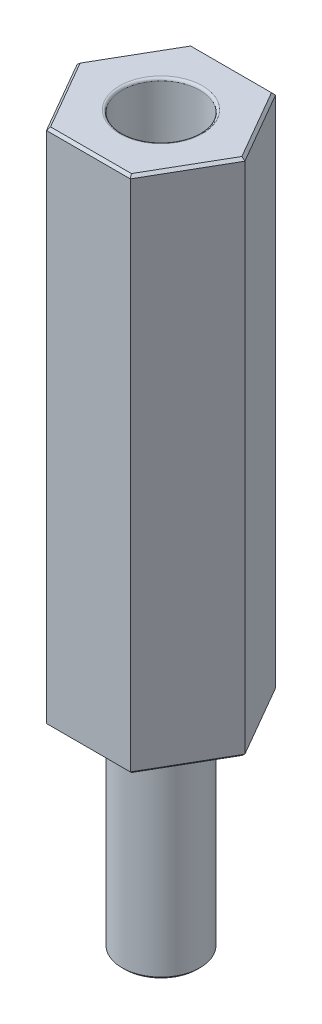
SolidWorks part; units mm, degrees
ref_plane "Front Plane" through (0, 0, 0) normal (0, 0, 1) x (1, 0, 0)
ref_plane "Top Plane" through (0, 0, 0) normal (0, 1, 0) x (1, 0, 0)
ref_plane "Right Plane" through (0, 0, 0) normal (1, 0, 0) x (0, 0, -1)
ref_plane "Plane1" through (0, 0, 0) normal (0, -1, 0) x (1, 0, 0)
sketch "Sketch1" plane through (0, 0, 0) normal (0, -1, 0) x (1, 0, 0)
  line L0 (-1.6166, 2.8) -> (-3.2332, 0)
  line L1 (-3.2332, 0) -> (-1.6166, -2.8)
  line L2 (-1.6166, -2.8) -> (1.6166, -2.8)
  line L3 (1.6166, -2.8) -> (3.2332, 0)
  line L4 (3.2332, 0) -> (1.6166, 2.8)
  line L5 (1.6166, 2.8) -> (-1.6166, 2.8)
extrude "Boss-Extrude1" add sketch "Sketch1" against normal blind 20
sketch "Sketch2" plane through (0, 0, 0) normal (0, 0, 1) x (1, 0, 0)
  line L0 (1.5, 0) -> (0, 0)
  line L1 (0, 0) -> (0, -8)
  line L2 (0, -8) -> (1.5, -8)
  line L3 (1.5, -8) -> (1.5, 0)
  line L4 (0, 0) -> (0, -8) construction
revolve "Revolve1" add sketch "Sketch2" angle 360 about L4
hole_wizard "Ø3.0mm Dowel Hole1" positions "Sketch4" profile "Sketch3" hole size "Ø3.0" standard "ANSI Metric"
sketch "Sketch4" plane through (0, 20, 0) normal (0, 1, 0) x (1, 0, 0)
  point P0 (0, 0)
sketch "Sketch3" plane through (0, 20, 0) normal (1, 0, 0) x (0, 0, 1)
  line L0 (0, 0) -> (0, 8.9013)
  line L1 (0, 8.9013) -> (1.5, 8)
  line L2 (1.5, 8) -> (1.5, 0)
  line L5 (1.5, 0) -> (0, 0)
  line L10 (0, 8.9013) -> (-1.5, 8) construction
  line L11 (0, -6.35) -> (0, 107.95) construction
  dimension "Hole Dia." = 3
  dimension "Hole Depth" = 8
  dimension "Drill Angle" = 118
fillet "Fillet1" radius 0.1 1 edges at (0, 20, 1.5)
chamfer "Chamfer1" distance 0.1 angle 45 13 edges at (1.5, -8, 0) (0, 0, -2.8) (-2.4249, 0, -1.4) (-2.4249, 0, 1.4) (0, 0, 2.8) (2.4249, 0, -1.4) (2.4249, 0, 1.4) (-2.4249, 20, 1.4) (-2.4249, 20, -1.4) (0, 20, -2.8) (2.4249, 20, -1.4) (2.4249, 20, 1.4) (0, 20, 2.8)
